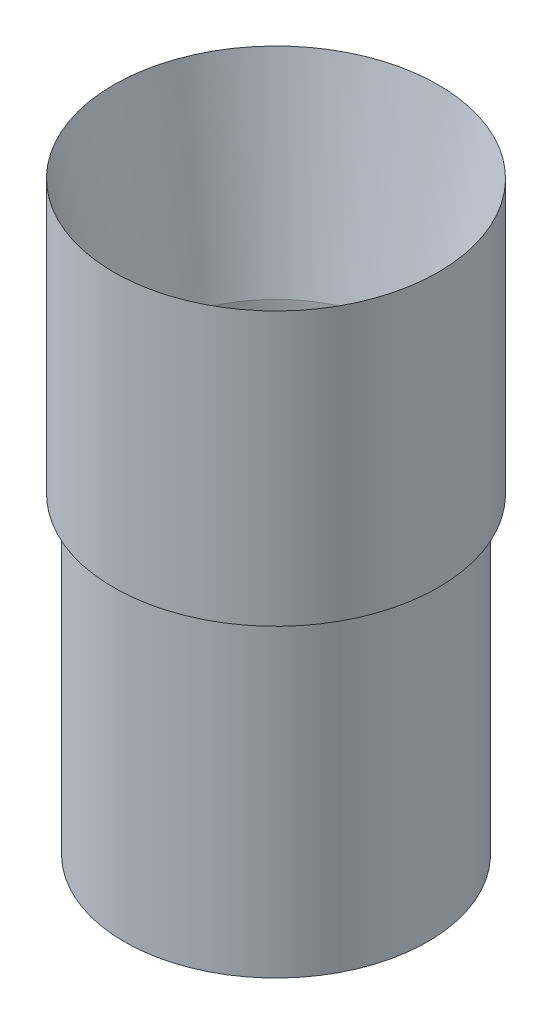
SolidWorks part; units mm, degrees
material "6061-T6 (SS)"
ref_plane "Front Plane" through (0, 0, 0) normal (0, 0, 1) x (1, 0, 0)
ref_plane "Top Plane" through (0, 0, 0) normal (0, 1, 0) x (1, 0, 0)
ref_plane "Right Plane" through (0, 0, 0) normal (1, 0, 0) x (0, 0, -1)
sketch "Sketch1" plane through (0, 0, 0) normal (0, 0, 1) x (1, 0, 0)
  line L13 (2.032, 0) -> (0, 0)
  line L15 (7.7424, 101.6) -> (2.032, 101.6)
  line L16 (2.032, 101.6) -> (2.032, 0)
  line L19 (-3.4544, 190.5) -> (-3.4544, 101.6)
  line L20 (-3.4544, 101.6) -> (0, 101.6)
  line L21 (0, 101.6) -> (0, 0)
  line L22 (49.3776, 245.6415) -> (49.3776, -77.8061) construction
  line L23 (7.7424, 127) -> (7.7424, 101.6)
  line L24 (7.7424, 127) -> (-3.4544, 190.5)
  dimension "D1" = 10
  dimension "D2" = 25.4
  dimension "D3" = 49.3776
  dimension "D4" = 2.032
  dimension "D5" = 101.6
  dimension "D6" = 101.6
  dimension "D7" = 88.9
  dimension "D8" = 52.832
revolve "Revolve1" add sketch "Sketch1" angle 360 about L22
